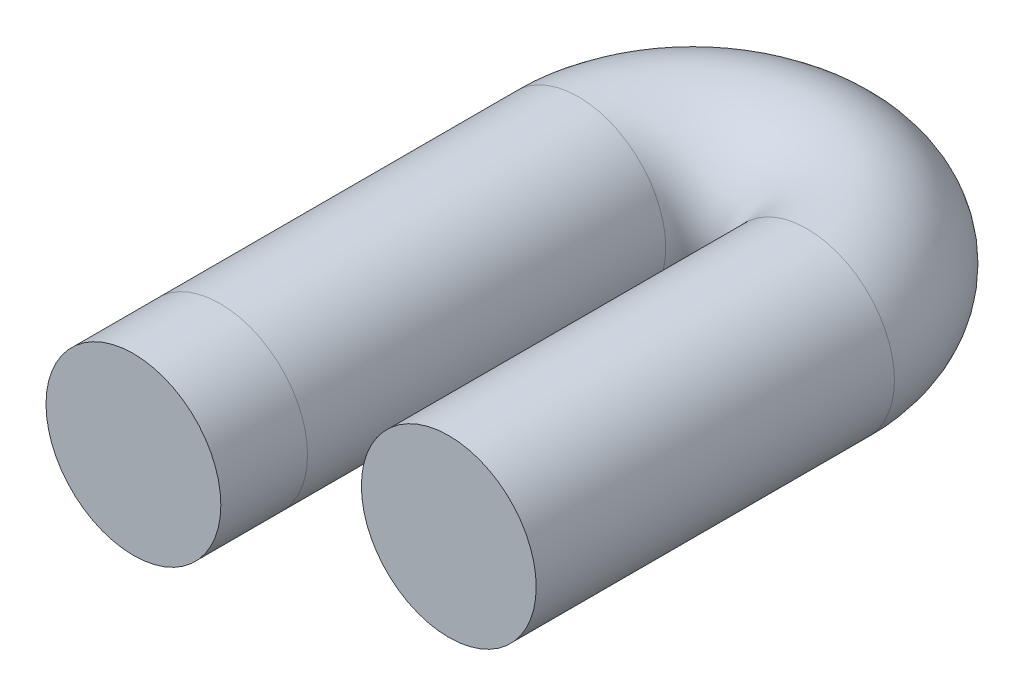
SolidWorks part; units mm, degrees
ref_plane "Front Plane" through (0, 0, 0) normal (0, 0, 1) x (1, 0, 0)
ref_plane "Top Plane" through (0, 0, 0) normal (0, 1, 0) x (1, 0, 0)
ref_plane "Right Plane" through (0, 0, 0) normal (1, 0, 0) x (0, 0, -1)
sketch "Sketch2" plane through (0, 0, 0) normal (0, 0, 1) x (1, 0, 0)
  circle A0 centre (0, 0) radius 20.9033
sketch "Sketch3" plane through (0, 0, 0) normal (0, 1, 0) x (1, 0, 0)
  line L0 (0, 0) -> (0, 20.7306)
  line L1 (0, 20.7306) -> (0, 106.3956)
  line L2 (54.6841, 106.3956) -> (54.6841, 20.7306)
  arc A0 (0, 106.3956) -> (54.6841, 106.3956) centre (27.342, 106.3956) cw
sweep "Sweep2" add profiles "Sketch2" path "Sketch3"
